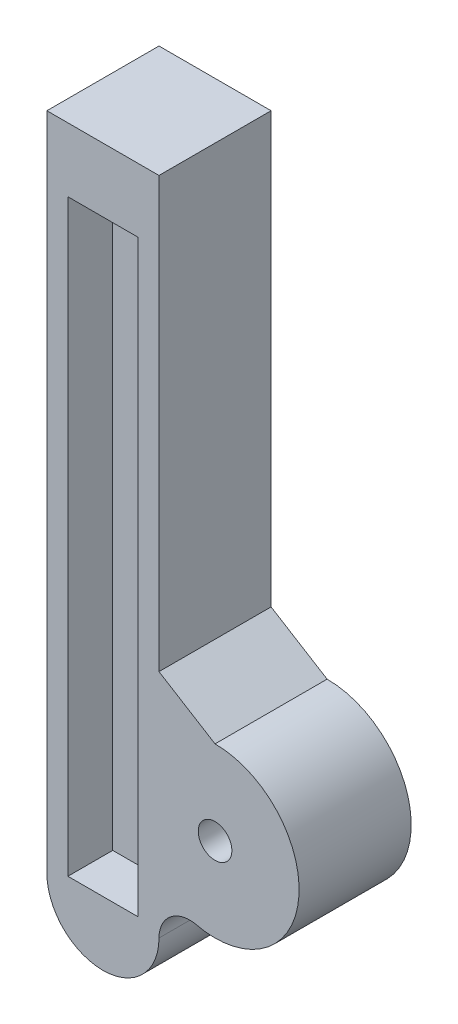
SolidWorks part; units mm, degrees
material "Custom Plastic"
ref_plane "Front Plane" through (0, 0, 0) normal (0, 0, 1) x (1, 0, 0)
ref_plane "Top Plane" through (0, 0, 0) normal (0, 1, 0) x (1, 0, 0)
ref_plane "Right Plane" through (0, 0, 0) normal (1, 0, 0) x (0, 0, -1)
other "Center of Mass"
sketch "Sketch1" plane through (0, 0, 0) normal (0, 1, 0) x (1, 0, 0)
  line L1 (-20, 30) -> (97.83, 30)
  line L2 (97.83, 10) -> (21.1605, 10)
  line L3 (15, 0) -> (21.1605, 10)
  line L4 (97.83, 30) -> (97.83, 10)
  arc A0 (-14.5171, 3.7753) -> (15, 0) centre (0, 0) ccw
  arc A1 (-20, 10) -> (-20, 30) centre (-20, 20) cw
  circle A3 centre (0, 0) radius 3
  arc A4 (-20, 10) -> (-14.5171, 3.7753) centre (-20, 4.4729) cw
  dimension "D1" = 30
  dimension "D6" = 6
  dimension "D2" = 20
  dimension "D3" = 20
  dimension "D4" = 97.83
  dimension "D5" = 20
extrude "Boss-Extrude1" add sketch "Sketch1" along normal blind 20
scale "Scale1" [suppressed]
sketch "Sketch8" plane through (0, 0, 0) normal (0, -1, 0) x (1, 0, 0)
  line L1 (-18.585, -14) -> (86.415, -14)
  line L2 (-18.585, -14) -> (-18.585, -26.5)
  line L3 (-18.585, -26.5) -> (86.415, -26.5)
  line L4 (86.415, -14) -> (86.415, -26.5)
  line L5 (-18.585, -14) -> (86.415, -26.5) construction
  line L6 (-18.585, -26.5) -> (86.415, -14) construction
  point P0 (33.915, -20.25)
  dimension "D1" = 105
  dimension "D2" = 12.5
extrude "Cut-Extrude7" cut sketch "Sketch8" against normal blind 8
sketch "Sketch9" plane through (0, 20, 0) normal (0, 1, 0) x (1, 0, 0)
  line L1 (-18.585, 26.25) -> (86.415, 26.25)
  line L2 (-18.585, 26.25) -> (-18.585, 13.75)
  line L3 (-18.585, 13.75) -> (86.415, 13.75)
  line L4 (86.415, 26.25) -> (86.415, 13.75)
  line L5 (-18.585, 26.25) -> (86.415, 13.75) construction
  line L6 (-18.585, 13.75) -> (86.415, 26.25) construction
  point P0 (33.915, 20)
  point P5 (86.415, 20)
  dimension "D1" = 105
  dimension "D2" = 12.5
extrude "Cut-Extrude8" cut sketch "Sketch9" against normal blind 8
move or copy body "Body-Move/Copy1" bodies to move or copy 110 copy no rotation origin (0, 10, -7.5) rotation axis (-1, 0, 0) rotation angle 90
move or copy body "Body-Move/Copy2" bodies to move or copy 111 copy no rotation origin (0, 10, -7.5) rotation axis (1, 0, 0) rotation angle 180
sketch "Sketch10" plane through (0, 0, 2.5) normal (0, 0, 1) x (1, 0, 0)
  point P0 (0, 2.5)
move or copy body "Body-Move/Copy5" bodies to move or copy 112 copy no translate (0, -2.5, -2.5)
move or copy body "Body-Move/Copy6" bodies to move or copy 115 copy no rotation origin (33.915, 7.5, 0) rotation axis (0, 0, 1) rotation angle 90
sketch "Sketch11" plane through (0, 0, 0) normal (0, 0, 1) x (1, 0, 0)
  point P0 (41.415, -26.415)
move or copy body "Body-Move/Copy7" bodies to move or copy 116 copy no translate (-41.415, 26.415, 0)
